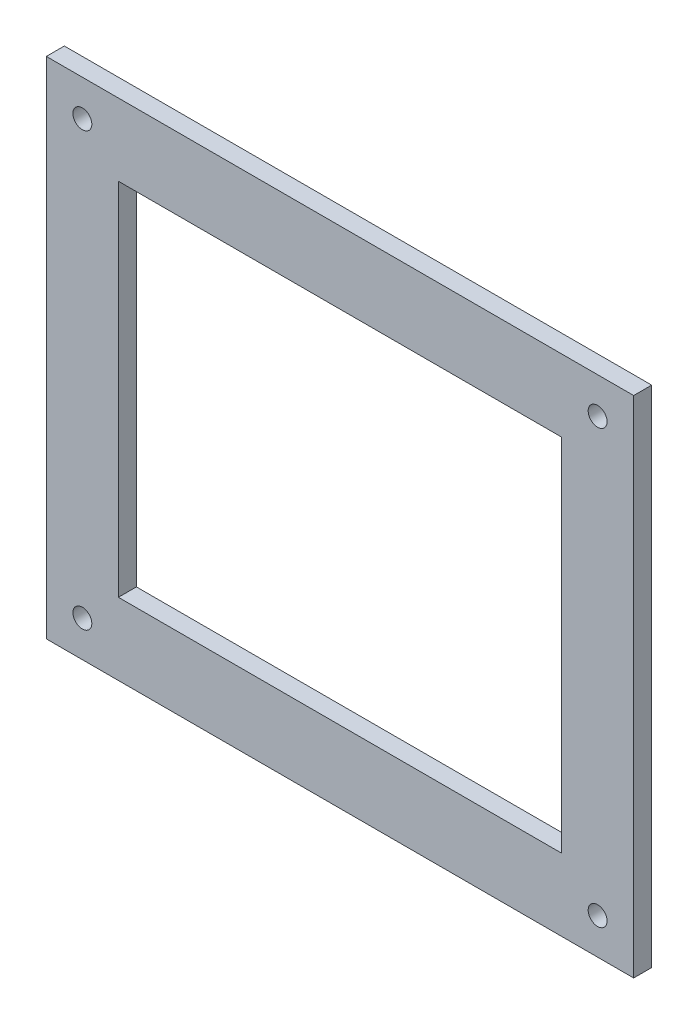
SolidWorks part; units mm, degrees
ref_plane "Front Plane" through (0, 0, 0) normal (0, 0, 1) x (1, 0, 0)
ref_plane "Top Plane" through (0, 0, 0) normal (0, 1, 0) x (1, 0, 0)
ref_plane "Right Plane" through (0, 0, 0) normal (1, 0, 0) x (0, 0, -1)
sketch "Sketch1" plane through (0, 0, 0) normal (0, 0, 1) x (1, 0, 0)
  line L0 (-40, -40) -> (286, -40)
  line L1 (0, 0) -> (246, 0)
  line L2 (0, 0) -> (0, 200)
  line L3 (0, 200) -> (246, 200)
  line L4 (246, 0) -> (246, 200)
  line L5 (286, -40) -> (286, 240)
  line L6 (-40, 240) -> (286, 240)
  line L7 (-40, -40) -> (-40, 240)
  line L8 (-20, -20) -> (266, -20) construction
  line L9 (266, -20) -> (266, 220) construction
  line L10 (-20, 220) -> (266, 220) construction
  line L11 (-20, -20) -> (-20, 220) construction
  circle A0 centre (-20, 220) radius 5.25
  circle A1 centre (266, 220) radius 5.25
  circle A2 centre (266, -20) radius 5.25
  circle A3 centre (-20, -20) radius 5.25
  dimension "D5" = 10.5
  dimension "D1" = 200
  dimension "D2" = 246
  dimension "D3" = 40
  dimension "D4" = 20
extrude "Boss-Extrude1" add sketch "Sketch1" along normal blind 10
